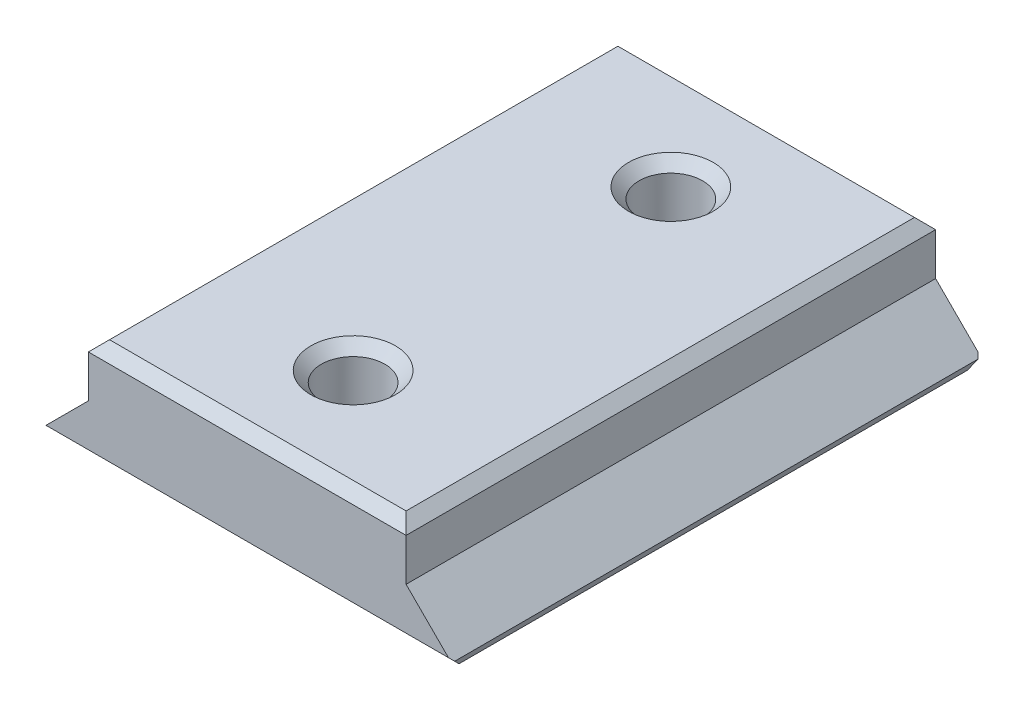
SolidWorks part; units mm, degrees
material "1060 合金"
ref_plane "前视基准面" through (0, 0, 0) normal (0, 0, 1) x (1, 0, 0)
ref_plane "上视基准面" through (0, 0, 0) normal (0, 1, 0) x (1, 0, 0)
ref_plane "右视基准面" through (0, 0, 0) normal (1, 0, 0) x (0, 0, -1)
other "Configuration Table"
sketch "草图2" plane through (0, 0, 0) normal (0, 0, 1) x (1, 0, 0)
  line L0 (0, 0) -> (15, 0)
  line L1 (15, 0) -> (15, -5)
  line L2 (15, -5) -> (20, -10)
  line L3 (20, -10) -> (-20, -10)
  line L4 (-20, -10) -> (-15, -5)
  line L5 (-15, -5) -> (-15, 0)
  line L6 (-15, 0) -> (0, 0)
  point P10 (-16.8472, -10.9952)
  dimension "D1" = 15
  dimension "D2" = 15
  dimension "D3" = 40
  dimension "D4" = 5
  dimension "D5" = 10
  dimension "D6" = 5
extrude "凸台-拉伸1" add sketch "草图2" along normal blind 50
sketch "草图4" plane through (0, -10, 0) normal (0, -1, 0) x (1, 0, 0)
  line L0 (-20, 0) -> (20, 0) construction
  line L1 (-20, 50) -> (20, 50) construction
  line L2 (20, 50) -> (20, 0) construction
  circle A0 centre (0, 40) radius 3
  circle A1 centre (0, 10) radius 3
  dimension "D1" = 6
  dimension "D2" = 6
  dimension "D3" = 10
  dimension "D4" = 10
  dimension "D5" = 20
  dimension "D6" = 20
extrude "切除-拉伸1" cut sketch "草图4" against normal blind 50
chamfer "倒角1" distance 5 angle 45 1 edges at (3, -10, 10)
chamfer "倒角2" distance 5 angle 45 1 edges at (3, -10, 40)
chamfer "倒角4" distance 1 angle 45 6 edges at (0, 0, 37) (0, 0, 7) (0, 0, 0) (-15, 0, 25) (15, 0, 25) (0, 0, 50)
chamfer "倒角5" distance 1 2 edges at (20, -10, 25) (-20, -10, 25)
chamfer "倒角6" distance 1 angle 45 2 edges at (0, -10, 0) (0, -10, 50)
